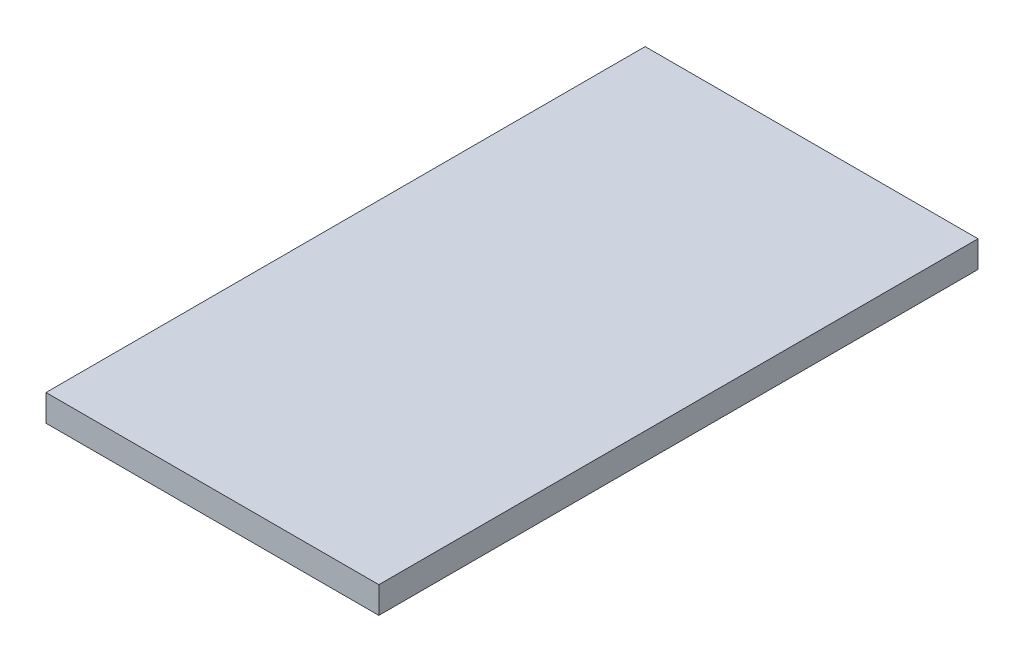
SolidWorks part; units mm, degrees
ref_plane "Front Plane" through (0, 0, 0) normal (0, 0, 1) x (1, 0, 0)
ref_plane "Top Plane" through (0, 0, 0) normal (0, 1, 0) x (1, 0, 0)
ref_plane "Right Plane" through (0, 0, 0) normal (1, 0, 0) x (0, 0, -1)
sketch "Sketch1" plane through (0, 0, 0) normal (0, 1, 0) x (1, 0, 0)
  line L1 (-12.5, 22.5) -> (12.5, 22.5)
  line L2 (-12.5, 22.5) -> (-12.5, -22.5)
  line L3 (-12.5, -22.5) -> (12.5, -22.5)
  line L4 (12.5, 22.5) -> (12.5, -22.5)
  line L5 (-12.5, 22.5) -> (12.5, -22.5) construction
  line L6 (-12.5, -22.5) -> (12.5, 22.5) construction
  point P0 (0, 0)
  dimension "D1" = 45
  dimension "D2" = 25
extrude "Boss-Extrude1" add sketch "Sketch1" along normal blind 2
